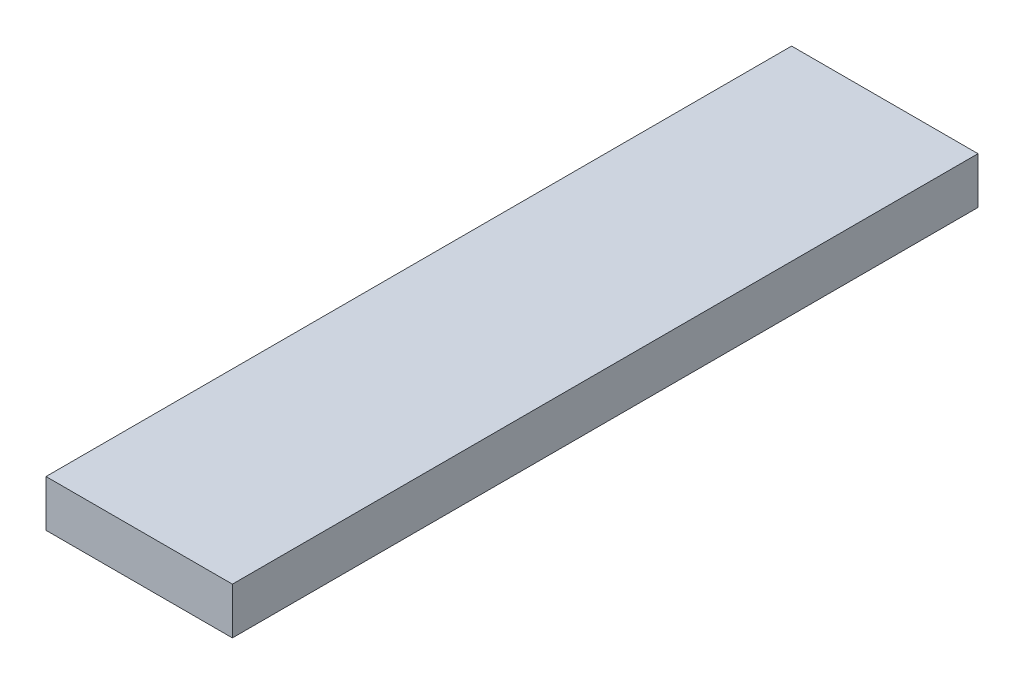
SolidWorks part; units mm, degrees
material "Gray Cast Iron"
ref_plane "Front Plane" through (0, 0, 0) normal (0, 0, 1) x (1, 0, 0)
ref_plane "Top Plane" through (0, 0, 0) normal (0, 1, 0) x (1, 0, 0)
ref_plane "Right Plane" through (0, 0, 0) normal (1, 0, 0) x (0, 0, -1)
sketch "Sketch1" plane through (0, 0, 0) normal (0, 1, 0) x (1, 0, 0)
  line L1 (41.1335, 921.3894) -> (541.1335, 921.3894)
  line L2 (41.1335, 921.3894) -> (41.1335, -1078.6106)
  line L3 (41.1335, -1078.6106) -> (541.1335, -1078.6106)
  line L4 (541.1335, 921.3894) -> (541.1335, -1078.6106)
  dimension "D1" = 2000
  dimension "D2" = 500
extrude "Boss-Extrude1" add sketch "Sketch1" along normal blind 125
